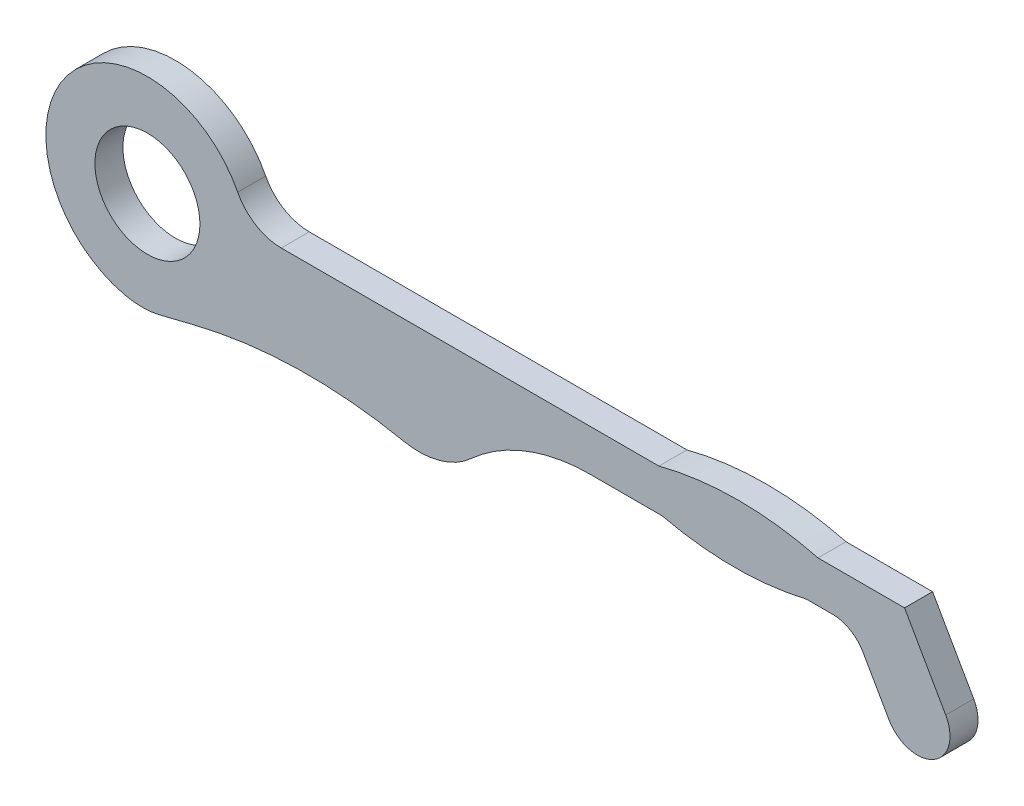
SolidWorks part; units mm, degrees
ref_plane "Alzado" through (0, 0, 0) normal (0, 0, 1) x (1, 0, 0)
ref_plane "Planta" through (0, 0, 0) normal (0, 1, 0) x (1, 0, 0)
ref_plane "Vista lateral" through (0, 0, 0) normal (1, 0, 0) x (0, 0, -1)
sketch "Sketch1" plane through (0, 0, 0) normal (0, 0, 1) x (1, 0, 0)
  line L0 (-1000, 0) -> (49000, 0) construction
  line L1 (-999.9504, 0.284) -> (49000.0496, 0.284) construction
  line L2 (-1000.0233, -0.309) -> (48999.9767, -0.309) construction
  line L3 (-999.0996, 4.058) -> (49000.9004, 4.058) construction
  line L4 (-999.2049, -0.979) -> (49000.7951, -0.979) construction
  line L5 (-999.2373, -2.838) -> (49000.7627, -2.838) construction
  line L6 (-999.3022, -4.094) -> (49000.6978, -4.094) construction
  line L7 (0, -1000) -> (0, 49000) construction
  line L8 (2.292, -1000.2374) -> (2.292, 48999.7626) construction
  line L9 (8.441, -1000.3832) -> (8.441, 48999.6168) construction
  line L10 (8.381, -1000.4642) -> (8.381, 48999.5358) construction
  line L11 (6.321, -999.4514) -> (6.321, 49000.5486) construction
  line L12 (10.995, -1000.0761) -> (10.995, 48999.9239) construction
  line L13 (-1007.9524, -7.872) -> (48992.0476, -7.872) construction
  line L14 (10.7077, 0.4679) -> (24772.2699, -43437.5918) construction
  line L15 (8.8604, 1.8226) -> (24770.4226, -43436.2371) construction
  line L16 (11.4007, -0.7477) -> (10.8126, 0.284)
  line L17 (10.0755, -0.309) -> (10.5893, -1.2103)
  line L18 (10.8126, 0.284) -> (9.5771, 0.284)
  line L19 (7.3049, 0.284) -> (1.4219, 0.284)
  line L20 (6.321, -0.309) -> (7.3502, -0.309)
  line L21 (0.0213, -1.4498) -> (0.659, -1.2916)
  line L22 (9.4118, -0.309) -> (10.0755, -0.309)
  arc A0 (1.4219, 0.284) -> (0.0213, -1.4498) centre (0, 0) ccw
  arc A1 (9.5771, 0.284) -> (7.3049, 0.284) centre (8.441, -4.094) ccw
  arc A2 (6.321, -0.309) -> (4.2533, -1.3819) centre (6.321, -2.838) ccw
  arc A3 (4.2533, -1.3819) -> (0.659, -1.2916) centre (2.292, -7.872) ccw
  arc A4 (10.5893, -1.2103) -> (11.4007, -0.7477) centre (10.995, -0.979) ccw
  arc A6 (7.3502, -0.309) -> (9.4118, -0.309) centre (8.381, 4.058) ccw
  arc A7 (0.0213, -1.4498) -> (0.659, -1.2916) centre (0, 0) ccw construction
  arc A8 (0.659, -1.2916) -> (0.1373, -1.4435) centre (2.292, -7.872) ccw construction
  point P28 (8.381, 4.058)
  point P31 (8.441, -4.094)
  point P33 (6.321, -2.838)
  point P34 (2.292, -7.872)
  point P35 (10.995, -0.979)
  dimension "D1" = 2.9
  dimension "D14" = 4.487
  dimension "D15" = 2.529
  dimension "D16" = 6.78
  dimension "D17" = 0.934
  dimension "D6" = 4.523
  dimension "D2" = 10.995
  dimension "D3" = 8.381
  dimension "D4" = 4.058
  dimension "D5" = 0.284
  dimension "D7" = 0.979
  dimension "D8" = 2.838
  dimension "D9" = 4.094
  dimension "D10" = 7.872
  dimension "D11" = 8.441
  dimension "D12" = 6.321
  dimension "D13" = 2.292
  dimension "D18" = 60.315
extrude "Boss-Extrude1" add sketch "Sketch1" along normal blind 0.4
sketch "Sketch2" plane through (0, 0, 0) normal (0, 0, 1) x (1, 0, 0)
  circle A0 centre (0, 0) radius 0.75
  dimension "D1" = 1.5
extrude "Cut-Extrude1" cut sketch "Sketch2" along normal up to next
fillet "Fillet1" radius 0.5 1 edges at (10.0755, -0.309, 0.2)
fillet "Fillet2" radius 0.7 1 edges at (1.4219, 0.284, 0.2)
fillet "Fillet3" radius 1.1 2 edges at (4.2533, -1.3819, 0.2) (0.0213, -1.4498, 0.2)
